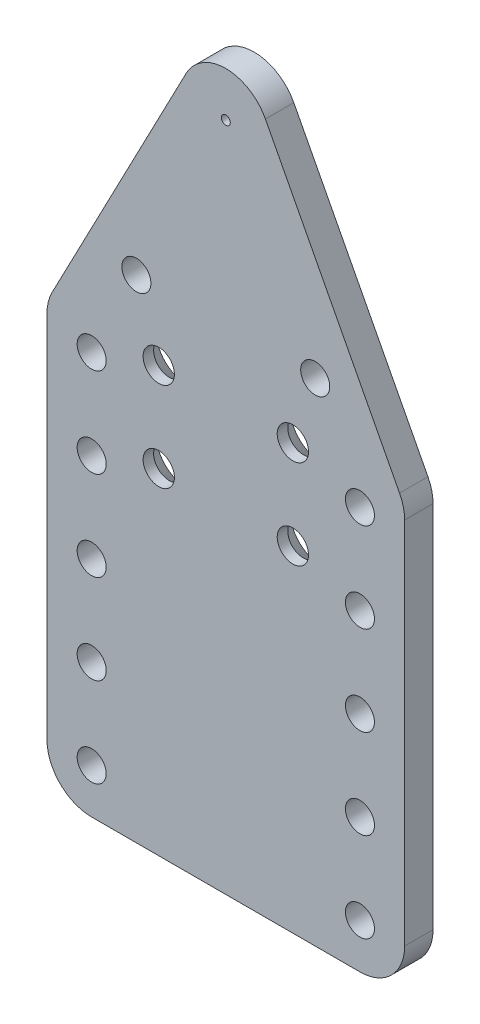
SolidWorks part; units mm, degrees
material "6061-T6 (SS)"
ref_plane "Front Plane" through (0, 0, 0) normal (0, 0, 1) x (1, 0, 0)
ref_plane "Top Plane" through (0, 0, 0) normal (0, 1, 0) x (1, 0, 0)
ref_plane "Right Plane" through (0, 0, 0) normal (1, 0, 0) x (0, 0, -1)
sketch "Sketch1" plane through (0, 0, 0) normal (0, 0, 1) x (1, 0, 0)
  line L0 (0, 0) -> (0, 112.5) construction
  line L1 (-40, 47.5) -> (-8.8643, 107.1286)
  line L3 (-40, -47.5) -> (40, -47.5)
  line L4 (-40, -47.5) -> (-40, 47.5)
  line L5 (-40, 47.5) -> (40, 47.5) construction
  line L6 (40, -47.5) -> (40, 47.5)
  line L7 (-40, -47.5) -> (40, 47.5) construction
  line L8 (-40, 47.5) -> (40, -47.5) construction
  line L9 (-15, 47.5) -> (15, 47.5) construction
  line L10 (-15, 47.5) -> (-15, 27.5) construction
  line L11 (-15, 27.5) -> (15, 27.5) construction
  line L12 (15, 47.5) -> (15, 27.5) construction
  line L13 (-15, 47.5) -> (15, 27.5) construction
  line L14 (8.8643, 107.1286) -> (40, 47.5)
  line L15 (15, 47.5) -> (-15, 27.5) construction
  line L17 (-22, 55) -> (22, 55) construction
  line L18 (-22, 55) -> (-22, 20) construction
  line L19 (-22, 20) -> (22, 20) construction
  line L20 (22, 55) -> (22, 20) construction
  line L21 (-22, 55) -> (22, 20) construction
  line L22 (-22, 20) -> (22, 55) construction
  circle A0 centre (-15, 47.5) radius 3.5
  circle A1 centre (15, 47.5) radius 3.5
  circle A2 centre (-15, 27.5) radius 3.5
  circle A3 centre (15, 27.5) radius 3.5
  arc A6 (8.8643, 107.1286) -> (-8.8643, 107.1286) centre (0, 102.5) ccw
  point P21 (0, 37.5)
  point P23 (0, 37.5)
  dimension "D4" = 7
  dimension "D8" = 10
  dimension "D1" = 80
  dimension "D2" = 30
  dimension "D3" = 20
  dimension "D9" = 65
  dimension "D10" = 95
  dimension "D11" = 35
  dimension "D12" = 44
extrude "Boss-Extrude1" add sketch "Sketch1" along normal blind 6.35
sketch "Sketch2" plane through (0, 0, 6.35) normal (0, 0, 1) x (1, 0, 0)
  line L0 (-30, -37.5) -> (30, -37.5) construction
  line L1 (0, 0) -> (0, -37.5) construction
  line L2 (-40, -47.5) -> (40, -47.5) construction
  circle A0 centre (30, -37.5) radius 3.25
  circle A1 centre (-30, -37.5) radius 3.25
  arc A2 (8.8643, 107.1286) -> (-8.8643, 107.1286) centre (0, 102.5) ccw construction
  dimension "D1" = 6.5
  dimension "D2" = 60
  dimension "D3" = 10
  dimension "D4" = 140
extrude "Cut-Extrude1" cut sketch "Sketch2" against normal through all
pattern_linear "LPattern1" count 5 spacing 20 along (0, 1, 0) of "Cut-Extrude1"
fillet "Fillet1" radius 10 4 edges at (40, 47.5, 3.175) (-40, 47.5, 3.175) (40, -47.5, 3.175) (-40, -47.5, 3.175)
sketch "Sketch3" plane through (0, 0, 6.35) normal (0, 0, 1) x (1, 0, 0)
  line L0 (0, 0) -> (0, 62.5) construction
  line L1 (-20, 62.5) -> (20, 62.5) construction
  circle A0 centre (-20, 62.5) radius 3.25
  circle A1 centre (20, 62.5) radius 3.25
  circle A2 centre (30, 42.5) radius 3.25 construction
  circle A3 centre (0, 102.5) radius 1
  dimension "D1" = 40
  dimension "D2" = 20
  dimension "D3" = 6.5
  dimension "D4" = 2
extrude "Cut-Extrude2" cut sketch "Sketch3" against normal through all
chamfer "Chamfer1" distance 4 angle 41 4 edges at (-11.5, 47.5, 0) (18.5, 47.5, 0) (18.5, 27.5, 0) (-11.5, 27.5, 0)
